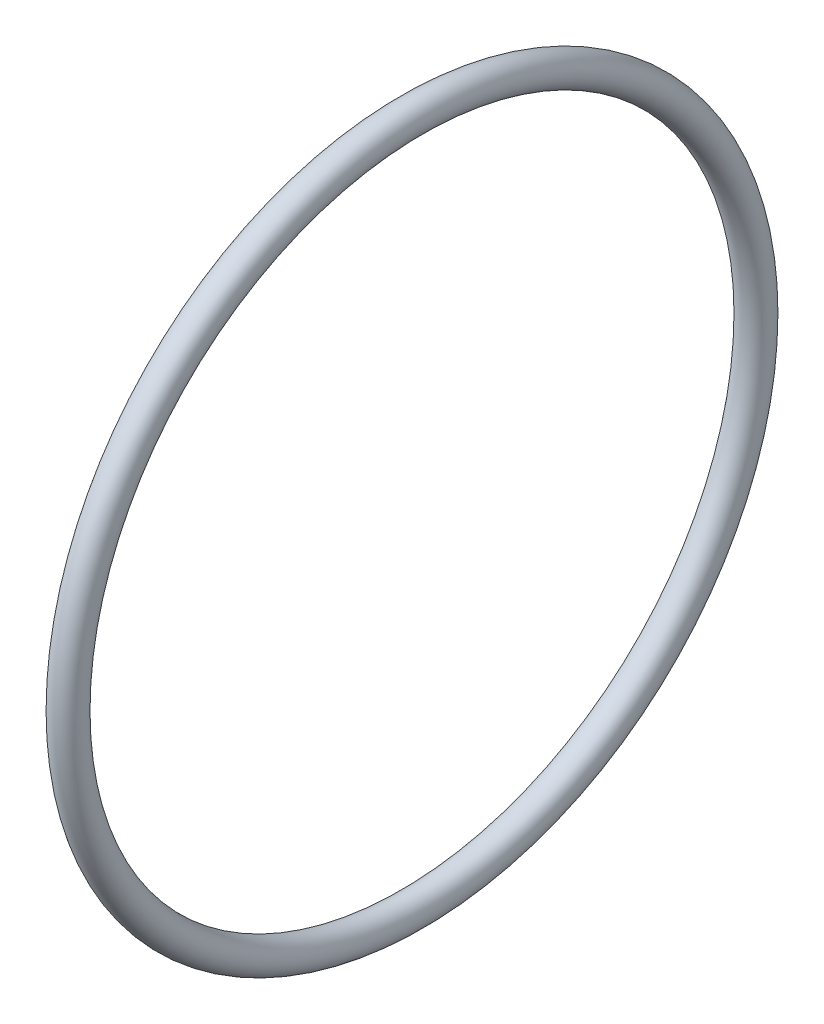
SolidWorks part; units mm, degrees
ref_plane "Front Plane" through (0, 0, 0) normal (0, 0, 1) x (1, 0, 0)
ref_plane "Top Plane" through (0, 0, 0) normal (0, 1, 0) x (1, 0, 0)
ref_plane "Right Plane" through (0, 0, 0) normal (1, 0, 0) x (0, 0, -1)
sketch "Sketch1" [suppressed] plane through (0, 0, 0) normal (0, 0, 1) x (1, 0, 0)
  line L0 (-43.7166, 0) -> (79.6876, 0) construction
  line L2 (0, -13.462) -> (1.524, -13.462)
  line L3 (0, -13.462) -> (0, -18.161)
  line L4 (0, -18.161) -> (1.524, -18.161)
  line L5 (1.524, -13.462) -> (1.524, -18.161)
  dimension "A" = 50.038
  dimension "B" = 58.42
  dimension "C" = 2.032
revolve "Revolve1" [suppressed] add sketch "Sketch1" angle 360 about L0
sketch "Sketch2" plane through (0, 0, 0) normal (0, 0, 1) x (1, 0, 0)
  line L0 (-34.685, 0) -> (47.6686, 0) construction
  circle A0 centre (2.54, -22.479) radius 1.016
  dimension "D1" = 2.54
  dimension "E" = 2.032
  dimension "D" = 42.926
revolve "Revolve3" add sketch "Sketch2" angle 360 about L0
